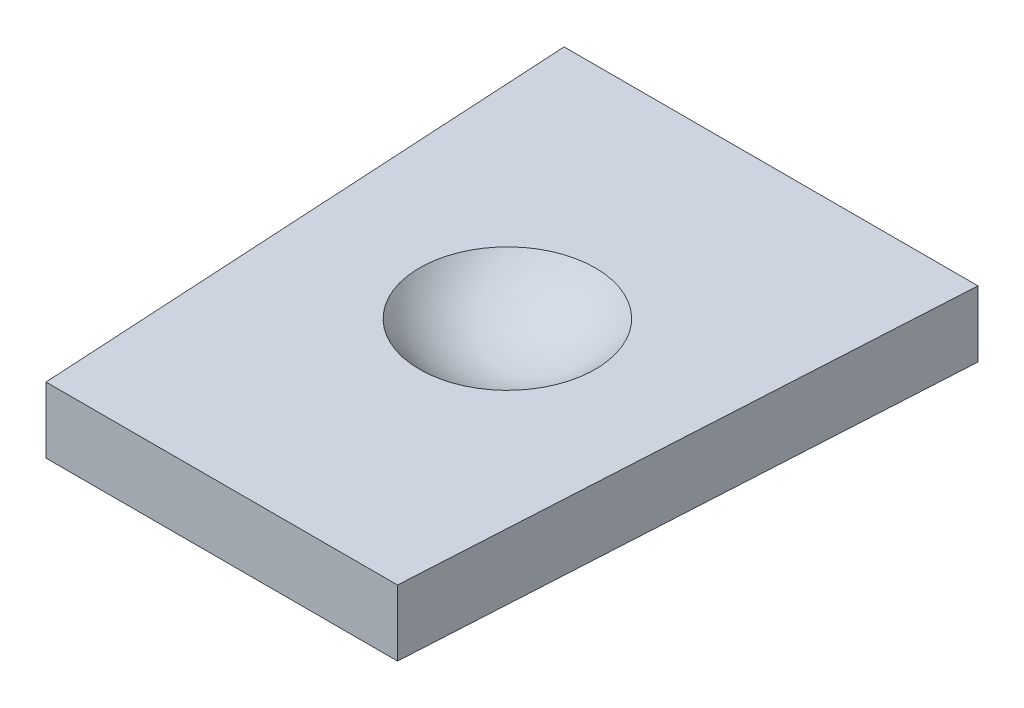
SolidWorks part; units mm, degrees
ref_plane "Front Plane" through (0, 0, 0) normal (0, 0, 1) x (1, 0, 0)
ref_plane "Top Plane" through (0, 0, 0) normal (0, 1, 0) x (1, 0, 0)
ref_plane "Right Plane" through (0, 0, 0) normal (1, 0, 0) x (0, 0, -1)
sketch "Sketch1" plane through (0, 0, 0) normal (0, 1, 0) x (1, 0, 0)
  line L0 (-9.4196, 89.5) -> (-8, 64.5)
  line L5 (-9.4196, 89.5) -> (0, 89.5)
  line L6 (0, 89.5) -> (0, 64.5)
  line L7 (0, 64.5) -> (-8, 64.5)
  point P4 (0, 77)
  dimension "D1" = 25
  dimension "D2" = 77
  dimension "D3" = 3.25
  dimension "D4" = 8
extrude "Boss-Extrude1" add sketch "Sketch1" along normal blind 3
mirror "Mirror1" about plane through (0, 0, 0) normal (1, 0, 0) of "Boss-Extrude1"
sketch "Sketch2" plane through (0, 0, 0) normal (1, 0, 0) x (0, 0, -1)
  line L0 (72.5, 6) -> (77.5, 6)
  line L1 (77.5, 6) -> (77.5, 1)
  arc A0 (72.5, 6) -> (77.5, 1) centre (77.5, 6) ccw
  dimension "D1" = 5
  dimension "D2" = 77.5
  dimension "D3" = 6
revolve "Cut-Revolve1" cut sketch "Sketch2" angle 360 about L1
